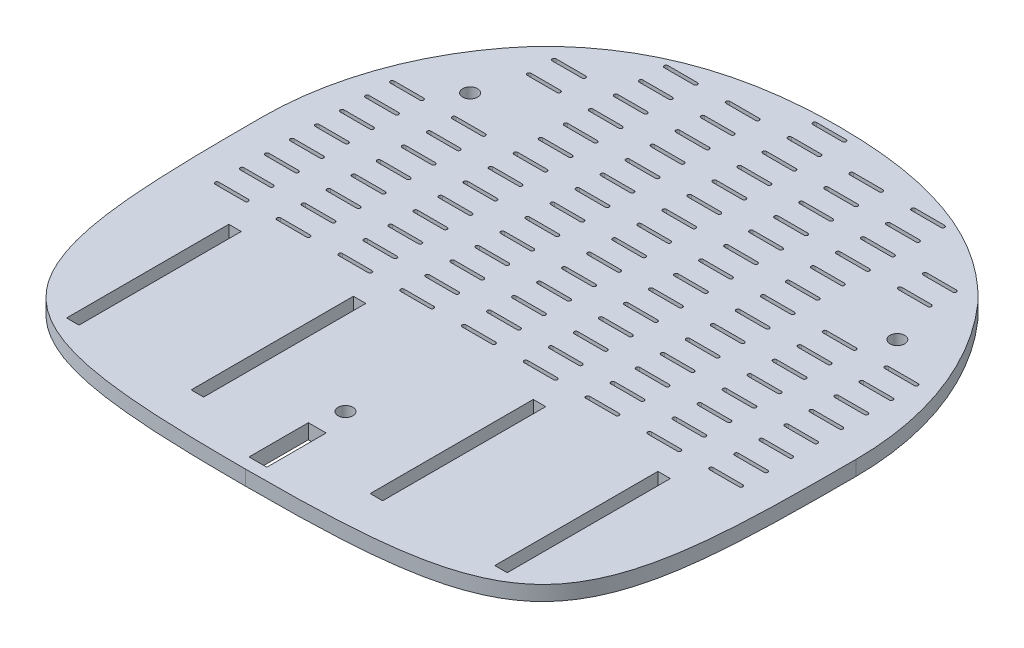
SolidWorks part; units mm, degrees
ref_plane "Front Plane" through (0, 0, 0) normal (0, 0, 1) x (1, 0, 0)
ref_plane "Top Plane" through (0, 0, 0) normal (0, 1, 0) x (1, 0, 0)
ref_plane "Right Plane" through (0, 0, 0) normal (1, 0, 0) x (0, 0, -1)
sketch "Layer1Limits" plane through (0, 0, 0) normal (0, 1, 0) x (1, 0, 0)
  line L0 (-127, 119.8228) -> (127, -134.1772) construction
  line L1 (-127, -134.1772) -> (127, -134.1772) construction
  line L2 (-127, -134.1772) -> (-127, 119.8228) construction
  line L3 (-127, 119.8228) -> (127, 119.8228) construction
  line L4 (127, -134.1772) -> (127, 119.8228) construction
  line L5 (127, 119.8228) -> (-127, -134.1772) construction
  line L6 (0, -1000) -> (0, 49000) construction
  point P4 (0, -7.1772)
  dimension "D1" = 254
  dimension "D2" = 254
sketch "Sketch1" plane through (0, 0, 0) normal (0, 1, 0) x (1, 0, 0)
  line L0 (0, 0) -> (-157.9039, -157.9039) construction
  line L1 (0, -134.1772) -> (0, 127) construction
  line L2 (-127, -134.1772) -> (127, -134.1772) construction
  arc A0 (127, 0) -> (-127, 0) centre (0, 0) ccw
  spline S0 degree 3 poles (-127, 0) (-127, -50.6247) (-125.8471, -127.4032) (-59.0891, -134.1772) (0, -134.1772) knots 0 0 0 0 0.496988 1 1 1 1
  spline S1 degree 3 poles (127, 0) (127, -50.6247) (125.8471, -127.4032) (59.0891, -134.1772) (0, -134.1772) knots 0 0 0 0 0.496988 1 1 1 1
  dimension "D1" = 254
extrude "Base" add sketch "Sketch1" along normal blind 6.35
sketch "Sketch16" plane through (0, 6.35, 0) normal (0, 1, 0) x (1, 0, 0)
  line L0 (0, -1000) -> (0, 49000) construction
  line L1 (-95.2696, 133.35) -> (-95.2696, 83.9803)
  line L2 (-95.2696, 133.35) -> (95.2696, 133.35)
  line L3 (95.2696, 133.35) -> (95.2696, 83.9803)
  arc A0 (127, 0) -> (-127, 0) centre (0, 0) ccw construction
  spline S0 degree 3 poles (-95.2696, 83.9803) (-69.156, 111.7112) (-34.9729, 119.8228) (0, 119.8228) knots 0 0 0 0 1 1 1 1
  spline S1 degree 3 poles (95.2696, 83.9803) (69.156, 111.7112) (34.9729, 119.8228) (0, 119.8228) knots 0 0 0 0 1 1 1 1
extrude "EmptySpaceTrim" cut sketch "Sketch16" against normal through all
sketch "ShaftLayout" plane through (0, 6.35, 0) normal (0, 1, 0) x (1, 0, 0)
  line L0 (-127, 0) -> (127, 0) construction
  line L1 (0, 133.35) -> (0, -127) construction
  line L2 (-114.7053, -6.35) -> (-104.7993, -6.35)
  line L3 (-36.3853, -38) -> (-94.3853, -38)
  line L4 (-36.3853, -38) -> (-36.3853, 38)
  line L5 (-36.3853, 38) -> (-94.3853, 38)
  line L6 (-94.3853, -38) -> (-94.3853, 38)
  line L7 (-36.3853, -38) -> (-94.3853, 38) construction
  line L8 (-36.3853, 38) -> (-94.3853, -38) construction
  line L9 (-102.0053, -15.875) -> (-104.7993, -15.875)
  line L10 (-102.0053, -15.875) -> (-102.0053, 15.875)
  line L11 (-102.0053, 15.875) -> (-104.7993, 15.875)
  line L12 (-104.7993, -15.875) -> (-104.7993, 15.875)
  line L13 (-102.0053, -15.875) -> (-104.7993, 15.875) construction
  line L14 (-102.0053, 15.875) -> (-104.7993, -15.875) construction
  line L15 (-114.7053, -6.35) -> (-114.7053, 6.35)
  line L16 (-104.7993, -6.35) -> (-104.7993, 6.35)
  line L17 (-114.7053, 6.35) -> (-104.7993, 6.35)
  line L18 (-114.7053, -6.35) -> (-104.7993, 6.35) construction
  line L19 (-104.7993, -6.35) -> (-114.7053, 6.35) construction
  line L20 (-116.2928, -9.525) -> (-114.7053, -9.525)
  line L21 (-116.2928, -9.525) -> (-116.2928, 9.525)
  line L22 (-114.7053, -9.525) -> (-114.7053, 9.525)
  line L23 (-116.2928, 9.525) -> (-114.7053, 9.525)
  line L24 (-116.2928, -9.525) -> (-114.7053, 9.525) construction
  line L25 (-114.7053, -9.525) -> (-116.2928, 9.525) construction
  line L26 (-127.4053, -7.9375) -> (-116.2928, -7.9375)
  line L27 (-127.4053, -7.9375) -> (-127.4053, 7.9375)
  line L28 (-116.2928, -7.9375) -> (-116.2928, 7.9375)
  line L29 (-127.4053, 7.9375) -> (-116.2928, 7.9375)
  line L30 (-127.4053, -7.9375) -> (-116.2928, 7.9375) construction
  line L31 (-116.2928, -7.9375) -> (-127.4053, 7.9375) construction
  line L32 (-17.3353, -7.9375) -> (-28.4478, -7.9375)
  line L33 (-30.0353, -9.525) -> (-28.4478, -9.525)
  line L34 (-30.0353, -9.525) -> (-30.0353, 9.525)
  line L35 (-30.0353, 9.525) -> (-28.4478, 9.525)
  line L36 (-28.4478, -9.525) -> (-28.4478, 9.525)
  line L37 (-30.0353, -9.525) -> (-28.4478, 9.525) construction
  line L38 (-30.0353, 9.525) -> (-28.4478, -9.525) construction
  line L39 (-17.3353, -7.9375) -> (-17.3353, 7.9375)
  line L40 (-28.4478, -7.9375) -> (-28.4478, 7.9375)
  line L41 (-17.3353, 7.9375) -> (-28.4478, 7.9375)
  line L42 (-17.3353, -7.9375) -> (-28.4478, 7.9375) construction
  line L43 (-28.4478, -7.9375) -> (-17.3353, 7.9375) construction
  line L45 (-67.3853, -10.033) -> (-56.3853, -10.033)
  line L46 (-67.3853, -10.033) -> (-67.3853, 10.033)
  line L47 (-67.3853, 10.033) -> (-56.3853, 10.033)
  line L48 (-56.3853, -10.033) -> (-56.3853, 10.033)
  line L49 (-67.3853, -10.033) -> (-56.3853, 10.033) construction
  line L50 (-67.3853, 10.033) -> (-56.3853, -10.033) construction
  point P10 (-65.3853, 0)
  point P15 (-103.4023, 0)
  point P20 (-29.2416, 0)
  point P21 (-109.7523, 0)
  point P22 (-115.4991, 0)
  point P23 (-121.8491, 0)
  point P40 (-61.8853, 0)
  point P41 (-22.8916, 0)
  dimension "D1" = 58
  dimension "D2" = 76
  dimension "D3" = 7.62
  dimension "D4" = 2.794
  dimension "D5" = 31.75
  dimension "D6" = 9.906
  dimension "D7" = 12.7
  dimension "D8" = 19.05
  dimension "D9" = 1.5875
  dimension "D10" = 12.7
  dimension "D11" = 15.875
  dimension "D12" = 19.05
  dimension "D13" = 1.5875
  dimension "D14" = 15.875
  dimension "D15" = 12.7
  dimension "D16" = 6.35
  dimension "D17" = 20.066
  dimension "D18" = 20
  dimension "D19" = 11
sketch "MotorLayout" plane through (0, 6.35, 0) normal (0, 1, 0) x (1, 0, 0)
  line L0 (-94.3853, -81.74) -> (-114.3853, -81.74) construction
  line L1 (-94.3853, -110.24) -> (-18.3853, -110.24)
  line L2 (-94.3853, -110.24) -> (-94.3853, -53.24)
  line L3 (-94.3853, -53.24) -> (-18.3853, -53.24)
  line L4 (-18.3853, -110.24) -> (-18.3853, -53.24)
  line L5 (-94.3853, -110.24) -> (-18.3853, -53.24) construction
  line L6 (-94.3853, -53.24) -> (-18.3853, -110.24) construction
  line L7 (-114.7053, -92.0587) -> (-104.7993, -92.0587)
  line L8 (-104.7993, -97.615) -> (-102.0053, -97.615)
  line L9 (-104.7993, -97.615) -> (-104.7993, -65.865)
  line L10 (-104.7993, -65.865) -> (-102.0053, -65.865)
  line L11 (-102.0053, -97.615) -> (-102.0053, -65.865)
  line L12 (-104.7993, -97.615) -> (-102.0053, -65.865) construction
  line L13 (-104.7993, -65.865) -> (-102.0053, -97.615) construction
  line L14 (-36.3853, -38) -> (-94.3853, -38) construction
  line L15 (-114.7053, -92.0587) -> (-114.7053, -71.4212)
  line L16 (-104.7993, -92.0587) -> (-104.7993, -71.4212)
  line L17 (-114.7053, -71.4212) -> (-104.7993, -71.4212)
  line L18 (-114.7053, -92.0587) -> (-104.7993, -71.4212) construction
  line L19 (-104.7993, -92.0587) -> (-114.7053, -71.4212) construction
  line L20 (-103.4023, -1000) -> (-103.4023, 49000) construction
  line L21 (-34.8953, -53.24) -> (-34.8953, -110.24) construction
  point P0 (-56.3853, -81.74)
  point P7 (-103.4023, -81.74)
  point P14 (-109.7523, -81.74)
  dimension "D1" = 20
  dimension "D2" = 76
  dimension "D3" = 57
  dimension "D4" = 2.794
  dimension "D5" = 15.24
  dimension "D6" = 31.75
  dimension "D7" = 20.6375
  dimension "D8" = 12.7
  dimension "D9" = 7.62
  dimension "D10" = 16.51
sketch "Sketch8" plane through (0, 6.35, 0) normal (0, 1, 0) x (1, 0, 0)
  line L0 (-94.3853, -81.74) -> (-18.3853, -81.74) construction
  line L1 (-18.3853, -110.24) -> (-18.3853, -53.24) construction
  line L2 (-94.3853, -53.24) -> (-18.3853, -53.24) construction
  line L3 (-35.7113, -116.463) -> (-41.0453, -116.463)
  line L4 (-35.7113, -116.463) -> (-35.7113, -47.017)
  line L5 (-35.7113, -47.017) -> (-41.0453, -47.017)
  line L6 (-41.0453, -116.463) -> (-41.0453, -47.017)
  line L7 (-35.7113, -116.463) -> (-41.0453, -47.017) construction
  line L8 (-35.7113, -47.017) -> (-41.0453, -116.463) construction
  line L9 (0, -1000) -> (0, 49000) construction
  line L10 (-94.3853, -110.24) -> (-18.3853, -110.24) construction
  line L11 (-3.81, -128.9302) -> (3.81, -128.9302)
  line L12 (89.0513, -46.763) -> (94.3853, -116.59) construction
  line L13 (89.0513, -116.59) -> (94.3853, -46.763) construction
  line L14 (35.7113, -46.763) -> (41.0453, -116.59) construction
  line L15 (-89.0513, -116.463) -> (-94.3853, -116.463)
  line L16 (-89.0513, -116.463) -> (-89.0513, -47.017)
  line L17 (-89.0513, -47.017) -> (-94.3853, -47.017)
  line L18 (-94.3853, -116.463) -> (-94.3853, -47.017)
  line L19 (-89.0513, -116.463) -> (-94.3853, -47.017) construction
  line L20 (-89.0513, -47.017) -> (-94.3853, -116.463) construction
  line L21 (-94.3853, -110.24) -> (-94.3853, -53.24) construction
  line L22 (-3.81, -128.9302) -> (-3.81, -103.5302)
  line L23 (35.7113, -116.59) -> (41.0453, -46.763) construction
  line L24 (-3.81, -103.5302) -> (3.81, -103.5302)
  line L25 (3.81, -128.9302) -> (3.81, -103.5302)
  line L26 (-3.81, -128.9302) -> (3.81, -103.5302) construction
  line L27 (-3.81, -103.5302) -> (3.81, -128.9302) construction
  line L29 (94.3853, -116.59) -> (94.3853, -46.763)
  line L30 (89.0513, -46.763) -> (94.3853, -46.763)
  line L31 (89.0513, -116.59) -> (89.0513, -46.763)
  line L32 (89.0513, -116.59) -> (94.3853, -116.59)
  line L33 (41.0453, -116.59) -> (41.0453, -46.763)
  line L34 (35.7113, -46.763) -> (41.0453, -46.763)
  line L35 (35.7113, -116.59) -> (35.7113, -46.763)
  line L36 (35.7113, -116.59) -> (41.0453, -116.59)
  point P6 (-63.7079, -81.74)
  point P7 (-38.2513, -81.74)
  point P16 (0, -116.2302)
  point P19 (-91.5913, -81.74)
  point P39 (91.5913, -81.74)
  point P40 (38.2513, -81.74)
  dimension "D1" = 5.334
  dimension "D2" = 6.223
  dimension "D4" = 7.62
  dimension "D5" = 25.4
  dimension "D6" = 6.223
  dimension "D3" = 2
extrude "MotorCut" cut sketch "Sketch8" against normal through all
sketch "Sketch11" plane through (0, 6.35, 0) normal (0, 1, 0) x (1, 0, 0)
  line L0 (0, -1000) -> (0, 49000) construction
  line L1 (-127, 0) -> (127, 0) construction
  circle A1 centre (0, -91.44) radius 3.175
  circle A2 centre (-91.44, 53.34) radius 3.175
  circle A3 centre (91.44, 53.34) radius 3.175
  dimension "D1" = 6.35
  dimension "D2" = 91.44
  dimension "D3" = 6.35
  dimension "D6" = 91.44
  dimension "D4" = 53.34
extrude "ScrewCut" cut sketch "Sketch11" against normal through all
sketch "Sketch17" plane through (0, 6.35, 0) normal (0, 1, 0) x (1, 0, 0)
  line L3 (-89.0513, -47.017) -> (-94.3853, -47.017) construction
  line L4 (-94.3853, -47.017) -> (-94.3853, -116.463) construction
  line L6 (-112.1653, -34.317) -> (-99.4653, -34.317) construction
  line L7 (-112.1653, -33.5232) -> (-99.4653, -33.5232)
  line L8 (-112.1653, -35.1107) -> (-99.4653, -35.1107)
  arc A1 (-112.1653, -33.5232) -> (-112.1653, -35.1107) centre (-112.1653, -34.317) ccw
  arc A2 (-99.4653, -35.1107) -> (-99.4653, -33.5232) centre (-99.4653, -34.317) ccw
  point P11 (-105.8153, -34.317)
  dimension "D1" = 12.7
  dimension "D2" = 1.5875
  dimension "D3" = 11.43
  dimension "D6" = 12.7
extrude "Cut-Extrude1" cut sketch "Sketch17" against normal through all
pattern_linear "LPattern1" count 9 spacing 26.4541 along (1, 0, 0) count 15 spacing 10.7188 along (0, 0, -1) skipping (0, 8), (0, 9), (0, 10), (0, 11), (0, 12), (0, 13), (0, 14), (1, 8), (1, 9), (1, 12), (1, 13), (1, 14), (2, 14), (3, 14), (5, 14), (6, 14), (7, 8), (7, 9), (7, 12), (7, 13), (7, 14), (8, 8), (8, 9), (8, 10), (8, 11), (8, 12), (8, 13), (8, 14) of "Cut-Extrude1"
